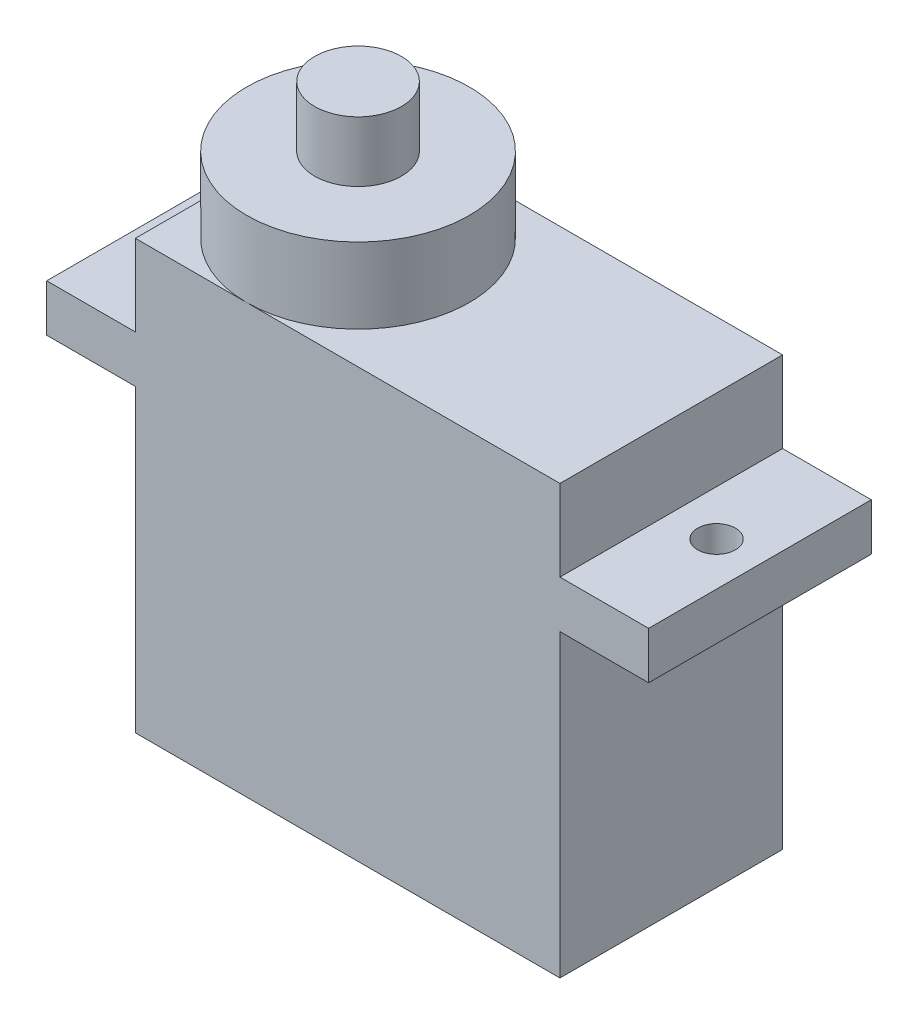
SolidWorks part; units mm, degrees
ref_plane "Front Plane" through (0, 0, 0) normal (0, 0, 1) x (1, 0, 0)
ref_plane "Top Plane" through (0, 0, 0) normal (0, 1, 0) x (1, 0, 0)
ref_plane "Right Plane" through (0, 0, 0) normal (1, 0, 0) x (0, 0, -1)
sketch "Sketch1" plane through (0, 0, 0) normal (0, 0, 1) x (1, 0, 0)
  line L1 (0, 0) -> (22.5, 0)
  line L2 (0, 0) -> (0, 22.7)
  line L3 (0, 22.7) -> (22.5, 22.7)
  line L4 (22.5, 0) -> (22.5, 22.7)
  line L5 (22.5, 15.9) -> (27.2, 15.9)
  line L6 (22.5, 15.9) -> (22.5, 18.4)
  line L7 (22.5, 18.4) -> (27.2, 18.4)
  line L8 (27.2, 15.9) -> (27.2, 18.4)
  line L12 (-4.7, 15.9) -> (0, 15.9)
  line L13 (-4.7, 15.9) -> (-4.7, 18.4)
  line L14 (-4.7, 18.4) -> (0, 18.4)
  line L15 (0, 15.9) -> (0, 18.4)
  dimension "D1" = 22.5
  dimension "D2" = 22.7
  dimension "D3" = 15.9
  dimension "D4" = 2.5
  dimension "D5" = 4.7
  dimension "D6" = 15.9
  dimension "D7" = 4.7
  dimension "D8" = 2.5
extrude "Boss-Extrude1" add sketch "Sketch1" along normal blind 11.8 contours L5 L8 L7 L4 | L1 L4 L3 L2 | L14 L13 L12 L2
sketch "Sketch3" plane through (0, 22.7, 0) normal (0, 1, 0) x (1, 0, 0)
  circle A0 centre (5.9, -5.9) radius 5.9
  circle A1 centre (5.9, -5.9) radius 2.3
  dimension "D2" = 11.8
  dimension "D4" = 4.6
  dimension "D1" = 5.9
  dimension "D3" = 5.9
extrude "Boss-Extrude2" add sketch "Sketch3" along normal blind 4 contours A0
sketch "Sketch5" plane through (0, 26.7, 0) normal (0, 1, 0) x (1, 0, 0)
  line L0 (0, -5.9) -> (11.8, -5.9)
  line L1 (0, -11.8) -> (0, 0) construction
  arc A0 (5.9, -11.8) -> (5.9, 0) centre (5.9, -5.9) ccw construction
  circle A1 centre (5.9, -5.9) radius 2.3
  dimension "D1" = 4.6
extrude "Boss-Extrude3" add sketch "Sketch5" along normal blind 3.2 contours L0 A1 | L0 A1
sketch "Sketch6" plane through (0, 18.4, 0) normal (0, 1, 0) x (1, 0, 0)
  line L0 (-4.7, -11.8) -> (-4.7, 0) construction
  line L1 (27.2, -11.8) -> (27.2, 0) construction
  line L2 (-4.7, -5.9) -> (27.2, -5.9) construction
  circle A0 centre (24.9, -5.9) radius 1
  circle A1 centre (-2.4, -5.9) radius 1
  dimension "D1" = 2
  dimension "D2" = 2
  dimension "D3" = 2.3
  dimension "D4" = 2.3
extrude "Cut-Extrude1" cut sketch "Sketch6" against normal blind 10
